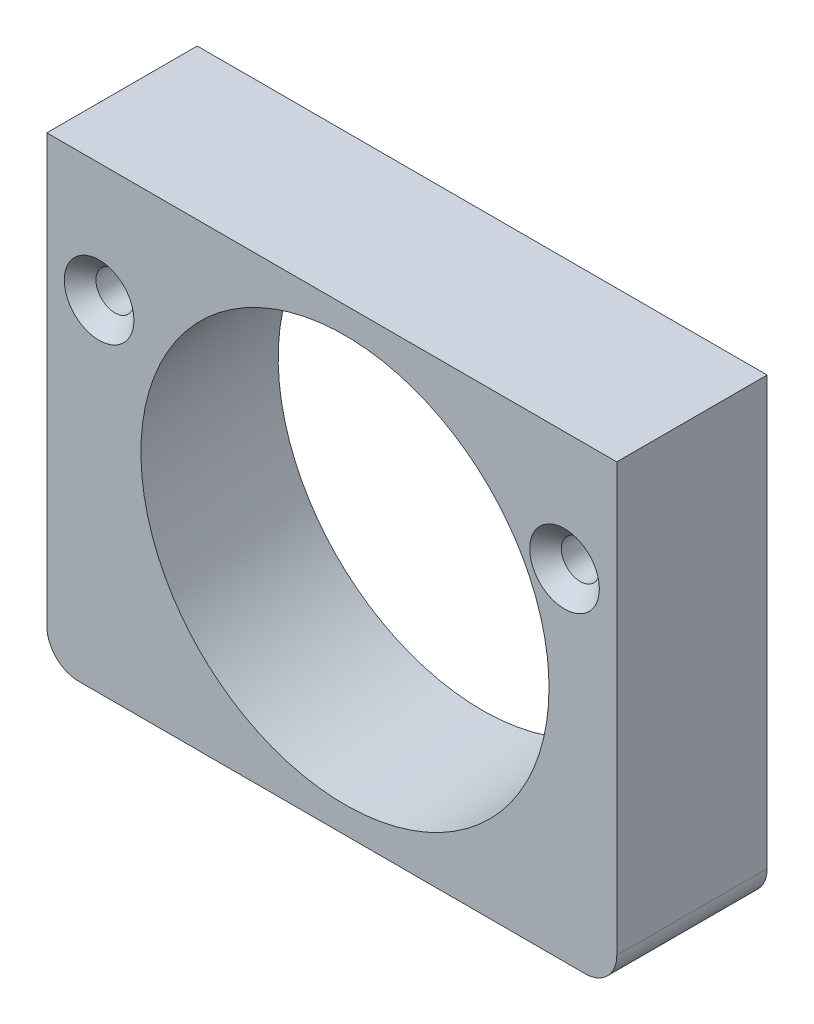
SolidWorks part; units mm, degrees
ref_plane "Front Plane" through (0, 0, 0) normal (0, 0, 1) x (1, 0, 0)
ref_plane "Top Plane" through (0, 0, 0) normal (0, 1, 0) x (1, 0, 0)
ref_plane "Right Plane" through (0, 0, 0) normal (1, 0, 0) x (0, 0, -1)
sketch "Sketch1" plane through (0, 0, 0) normal (0, 0, 1) x (1, 0, 0)
  line L1 (-16, -14.5) -> (16, -14.5)
  line L2 (-18, -12.5) -> (-18, 14.5)
  line L3 (-18, 14.5) -> (18, 14.5)
  line L4 (18, -12.5) -> (18, 14.5)
  line L5 (-18, -14.5) -> (18, 14.5) construction
  line L6 (-18, 14.5) -> (18, -14.5) construction
  arc A0 (16, -14.5) -> (18, -12.5) centre (16, -12.5) ccw
  arc A1 (-16, -14.5) -> (-18, -12.5) centre (-16, -12.5) cw
  point P0 (0, 0)
  dimension "D1" = 2
  dimension "D2" = 29
  dimension "D3" = 36
extrude "Boss-Extrude1" add sketch "Sketch1" along normal blind 9.5
ref_plane "Plane1" through (0.9616, 0, 10.9907) normal (0.0872, 0, 0.9962) x (0, 1, 0)
sketch "Sketch2" plane through (0.9616, 0, 10.9907) normal (0.0872, 0, 0.9962) x (0, 1, 0)
  circle A0 centre (0, 0) radius 12.8397
  dimension "D1" = 25.6794
extrude "Cut-Extrude1" cut sketch "Sketch2" against normal up to next
hole_wizard "CSK for M2 Countersunk Flat Head Screw1" positions "Sketch4" profile "Sketch5" countersink size "M2" standard "DIN" end condition up to next
sketch "Sketch4" plane through (0, 0, 9.5) normal (0, 0, 1) x (1, 0, 0)
  line L0 (18, 14.5) -> (-18, 14.5) construction
  line L1 (18, -12.5) -> (18, 14.5) construction
  line L2 (-18, 14.5) -> (-18, -12.5) construction
  point P0 (-14.7, 7)
  point P2 (14.7, 7)
  dimension "D1" = 7.5
  dimension "D2" = 3.3
  dimension "D3" = 3.3
sketch "Sketch5" plane through (-14.7, 7, 9.5) normal (1, 0, 0) x (0, -1, 0)
  line L0 (0, 0) -> (0, 9.5)
  line L1 (0, 9.5) -> (1.2, 9.5)
  line L2 (1.2, 9.5) -> (1.2, 1)
  line L3 (1.2, 1) -> (2.2, 0)
  line L5 (2.2, 0) -> (0, 0)
  line L6 (-1.2, 1) -> (-2.2, 0) construction
  line L11 (0, -6.35) -> (0, 107.95) construction
  dimension "Thru Hole Dia." = 2.4
  dimension "Thru Hole Depth" = 9.5
  dimension "Near C'Sink Dia." = 4.4
  dimension "Near C'Sink Angle" = 90
